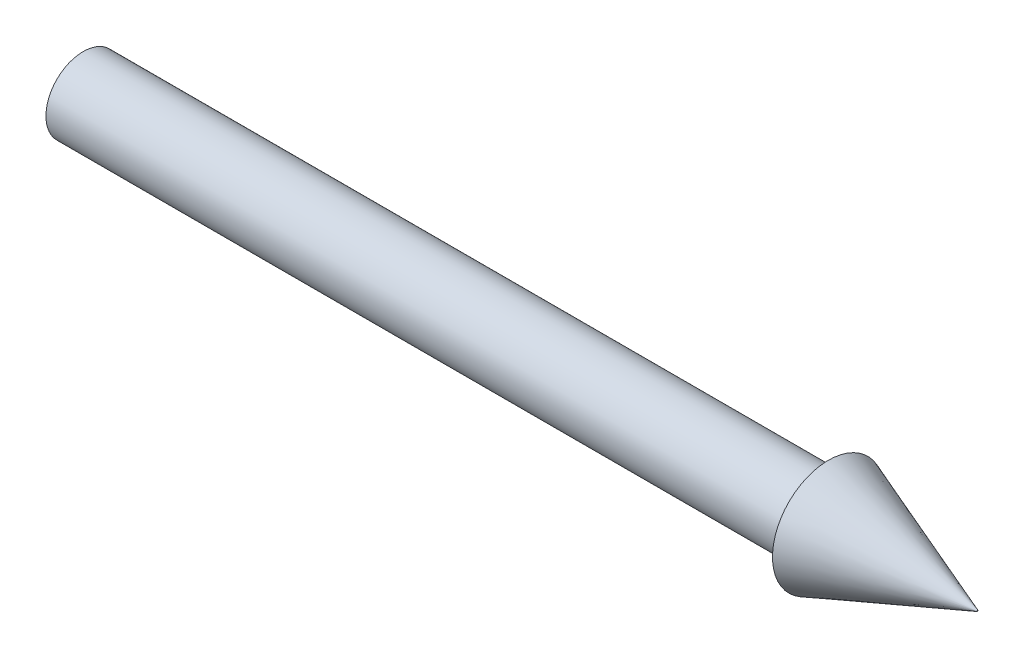
SolidWorks part; units mm, degrees
material "6061-T6 (SS)"
ref_plane "Front Plane" through (0, 0, 0) normal (0, 0, 1) x (1, 0, 0)
ref_plane "Top Plane" through (0, 0, 0) normal (0, 1, 0) x (1, 0, 0)
ref_plane "Right Plane" through (0, 0, 0) normal (1, 0, 0) x (0, 0, -1)
sketch "Sketch1" plane through (0, 0, 0) normal (1, 0, 0) x (0, 0, -1)
  circle A0 centre (0, 0) radius 12.7
  dimension "D1" = 25.4
extrude "Boss-Extrude1" add sketch "Sketch1" along normal mid plane 254
sketch "Sketch2" plane through (127, 0, 0) normal (1, 0, 0) x (0, 0, -1)
  circle A0 centre (0, 0) radius 19.05
  dimension "D1" = 38.1
ref_plane "Plane1" through (177.8, 0, 0) normal (1, 0, 0) x (0, 0, -1)
sketch "Sketch3" plane through (177.8, 0, 0) normal (1, 0, 0) x (0, 0, -1)
  circle A0 centre (0, 0) radius 0.1984
  dimension "D1" = 0.3969
loft "Loft1" add profiles "Sketch2", "Sketch3"
